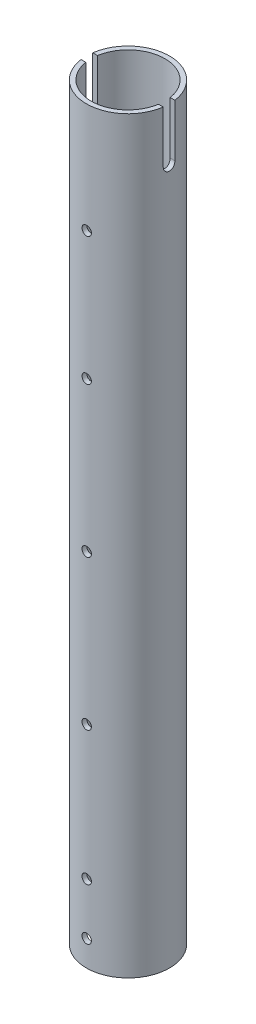
SolidWorks part; units mm, degrees
material "6061-T6 (SS)"
ref_plane "Front Plane" through (0, 0, 0) normal (0, 0, 1) x (1, 0, 0)
ref_plane "Top Plane" through (0, 0, 0) normal (0, 1, 0) x (1, 0, 0)
ref_plane "Right Plane" through (0, 0, 0) normal (1, 0, 0) x (0, 0, -1)
sketch "Sketch1" plane through (0, 0, 0) normal (0, 1, 0) x (1, 0, 0)
  circle A0 centre (0, 0) radius 25.0031
  circle A1 centre (0, 0) radius 28.1781
  dimension "D2" = 56.3562
  dimension "D1" = 3.175
extrude "Boss-Extrude1" add sketch "Sketch1" along normal blind 508
sketch "Sketch2" plane through (0, 0, 0) normal (0, -1, 0) x (1, 0, 0)
  line L0 (0, 28.1781) -> (0, 25.0031)
  circle A0 centre (0, 0) radius 28.1781 construction
  circle A1 centre (0, 0) radius 25.0031 construction
ref_plane "Plane1" through (0, 0, 28.1781) normal (0, 0, 1) x (1, 0, 0)
sketch "Sketch3" plane through (0, 0, 28.1781) normal (0, 0, 1) x (1, 0, 0)
  line L0 (-51.2718, 34.925) -> (56.5162, 34.925) construction
  line L1 (-28.1781, 0) -> (28.1781, 0) construction
  circle A0 centre (0, 17.4625) radius 3.175
  circle A1 centre (0, 52.3875) radius 3.175
  dimension "D2" = 6.35
  dimension "D1" = 34.925
  dimension "D3" = 17.4625
extrude "Cut-Extrude1" cut sketch "Sketch3" against normal through all
sketch "Sketch4" plane through (0, 0, 0) normal (0, 0, 1) x (1, 0, 0)
  circle A0 centre (0, 143.256) radius 3.175
  circle A1 centre (0, 244.856) radius 3.175
  circle A2 centre (0, 346.456) radius 3.175
  circle A4 centre (0, 433.5309) radius 3.175
  dimension "D1" = 143.256
  dimension "D4" = 6.35
  dimension "D5" = 6.35
  dimension "D6" = 6.35
  dimension "D2" = 101.6
  dimension "D3" = 203.2
extrude "Cut-Extrude2" cut sketch "Sketch4" against normal mid plane 120.904
ref_plane "Plane2" through (28.1781, 0, 0) normal (1, 0, 0) x (0, 0, -1)
sketch "Sketch6" plane through (28.1781, 0, 0) normal (1, 0, 0) x (0, 0, -1)
  line L0 (0, 508) -> (0, 472.44) construction
  line L1 (28.1781, 508) -> (-28.1781, 508) construction
  line L2 (3.9687, 508) -> (3.9688, 472.44)
  line L3 (-3.9687, 508) -> (-3.9687, 472.44)
  arc A0 (3.9687, 508) -> (-3.9687, 508) centre (0, 508) ccw
  arc A1 (-3.9687, 472.44) -> (3.9688, 472.44) centre (0, 472.44) ccw
  point P5 (0, 490.22)
  dimension "D2" = 3.9688
  dimension "D1" = 35.56
extrude "Cut-Extrude3" cut sketch "Sketch6" against normal through all
